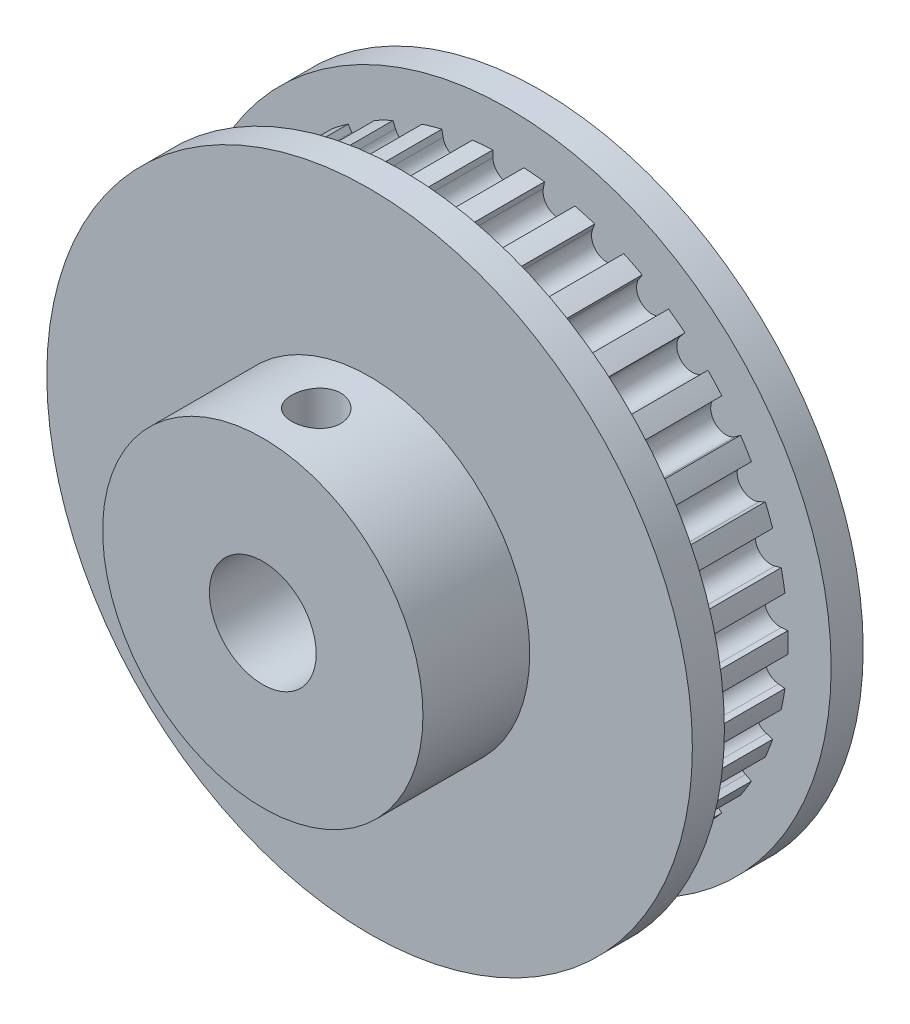
SolidWorks part; units mm, degrees
ref_plane "Front Plane" through (0, 0, 0) normal (0, 0, 1) x (1, 0, 0)
ref_plane "Top Plane" through (0, 0, 0) normal (0, 1, 0) x (1, 0, 0)
ref_plane "Right Plane" through (0, 0, 0) normal (1, 0, 0) x (0, 0, -1)
sketch "Sketch1" plane through (0, 0, 0) normal (0, 0, 1) x (1, 0, 0)
  line L3 (-1.4732, 27.9146) -> (1.4732, 27.9146) construction
  line L4 (0, 0) -> (0, 24.1046) construction
  line L5 (0, 24.1046) -> (0, 26.1874) construction
  line L6 (-1.4479, 25.5372) -> (-1.4732, 27.9146)
  line L7 (1.4479, 25.5372) -> (1.4732, 27.9146)
  line L8 (0, 26.1874) -> (0, 27.9146) construction
  circle A0 centre (0, 0) radius 27.051 construction
  circle A1 centre (0, 0) radius 30.23 construction
  arc A3 (-1.4479, 25.5372) -> (1.4479, 25.5372) centre (0, 25.5526) ccw
  point P11 (0, 27.051)
  point P13 (0, 30.23)
  dimension "D3" = 1.448
  dimension "D1" = 2.9464
  dimension "D2" = 3.81
sketch "Sketch2" plane through (0, 0, 0) normal (1, 0, 0) x (0, 0, -1)
  line L0 (-13, 5) -> (13, 5)
  line L1 (10, 26.1874) -> (10, 30.23)
  line L2 (-3, 15) -> (-13, 15)
  line L3 (13, 30.23) -> (10, 30.23)
  line L4 (-3, 30.23) -> (13, 30.23) construction
  line L5 (5, 30.23) -> (5, 26.1874) construction
  line L6 (0, 26.1874) -> (10, 26.1874)
  line L7 (0, 28.2087) -> (0, 30.23)
  line L8 (10, 28.2087) -> (10, 30.23) construction
  line L9 (13, 30.23) -> (13, 5)
  line L10 (-13, 0) -> (13, 0) construction
  line L11 (-13, 15) -> (-13, 5)
  line L12 (-3, 15) -> (-3, 30.23)
  line L13 (0, 30.23) -> (-1.5, 30.23)
  line L14 (17.1325, 30.23) -> (10, 30.23) construction
  line L15 (0, 26.1874) -> (0, 28.2087)
  line L16 (0, 28.2087) -> (0, 30.23) construction
  line L17 (0, 30.23) -> (-1.5, 30.23) construction
  line L18 (-1.5, 30.23) -> (-3, 30.23)
  point P25 (13, 0)
  point P26 (-3, 0)
  dimension "ID" = 10
  dimension "Hub Dia" = 30
  dimension "Outside Width" = 16
  dimension "Inside Width" = 10
  dimension "D2" = 60.46
revolve "Revolve1" add sketch "Sketch2" angle 360 mid plane about L10
sketch "Sketch3" plane through (0, 0, 0) normal (0, 0, 1) x (1, 0, 0)
  line L3 (-1.4479, 25.5372) -> (-1.4732, 27.9146) construction
  line L4 (1.4479, 25.5372) -> (1.4732, 27.9146) construction
  line L5 (-1.4479, 25.5372) -> (-1.4544, 26.147)
  line L6 (1.4479, 25.5372) -> (1.4544, 26.147)
  circle A0 centre (0, 0) radius 26.1874 construction
  arc A1 (1.4544, 26.147) -> (-1.4544, 26.147) centre (0, 0) ccw
  arc A3 (-1.4479, 25.5372) -> (1.4479, 25.5372) centre (0, 25.5526) ccw construction
  arc A4 (-1.4479, 25.5372) -> (1.4479, 25.5372) centre (0, 25.5526) ccw
extrude "Cut-Extrude1" cut sketch "Sketch3" against normal up to vertex (10 mm away) from vertex at 0 up to point (0, 26.1874, -10) starting at point (0, 26.1874, 0)
pattern_circular "CirPattern1" count 34 over 360 about axis through (0, 0, 0) along (0, 0, 1) of "Cut-Extrude1"
sketch "Sketch5" plane through (0, 0, 13) normal (0, 0, 1) x (1, 0, 0)
  line L0 (0, 0) -> (0, 3.25) construction
  line L1 (-3, 1.5) -> (3, 1.5)
  line L2 (-3, 1.5) -> (-3, 5)
  line L3 (-3, 5) -> (3, 5)
  line L4 (3, 1.5) -> (3, 5)
  line L5 (-3, 1.5) -> (3, 5) construction
  line L6 (-3, 5) -> (3, 1.5) construction
  circle A0 centre (0, 0) radius 5 construction
  point P0 (0, 3.25)
  dimension "D1" = 3.5
  dimension "D2" = 6
ref_plane "Plane1" through (0, 15, 0) normal (0, 1, 0) x (1, 0, 0)
sketch "Sketch4" plane through (0, 15, 0) normal (0, 1, 0) x (1, 0, 0)
  line L0 (0, -3) -> (0, -13) construction
  line L1 (-15, -3) -> (15, -3) construction
  line L2 (-15, -13) -> (15, -13) construction
  circle A0 centre (0, -8) radius 2.3
  dimension "D1" = 4.6
extrude "Cut-Extrude2" cut sketch "Sketch4" against normal blind 13
equation "\"D2@Sketch2\" =  \"OD@Sketch1\""
